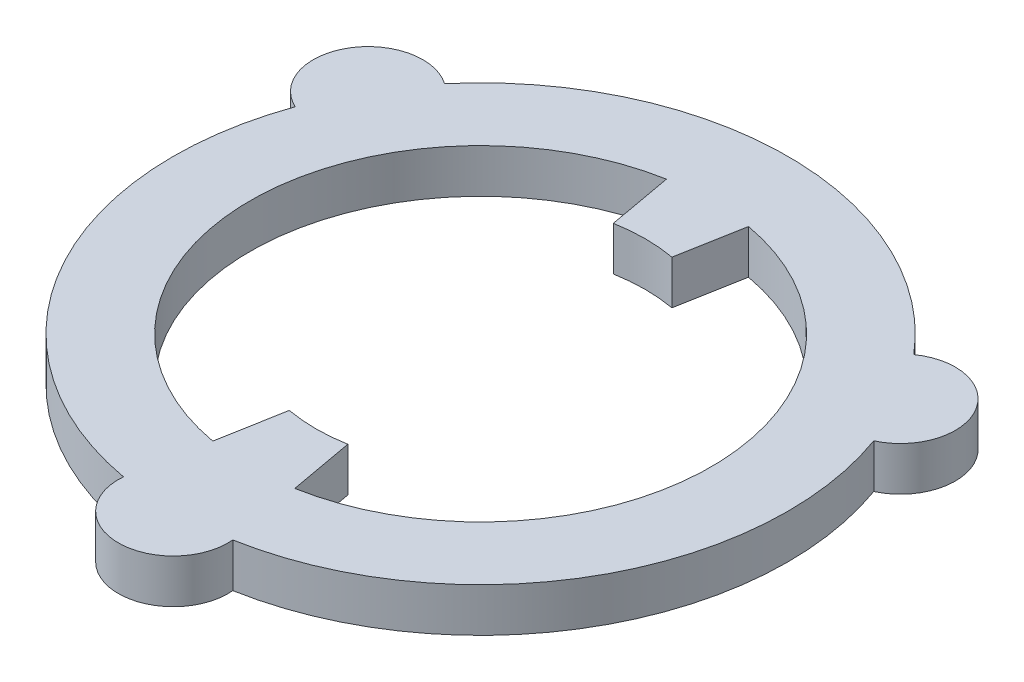
SolidWorks part; units mm, degrees
ref_plane "Planta" through (0, 0, 0) normal (0, 0, 1) x (1, 0, 0)
ref_plane "Alzado" through (0, 0, 0) normal (0, 1, 0) x (1, 0, 0)
ref_plane "Vista lateral" through (0, 0, 0) normal (1, 0, 0) x (0, 0, -1)
sketch "Croquis1" plane through (0, 0, 0) normal (0, 1, 0) x (1, 0, 0)
  line L0 (0, -9.3154) -> (0, -7.5) construction
  line L1 (0, 0) -> (-6.4952, 3.75) construction
  line L2 (0, 0) -> (12.1244, 7) construction
  line L4 (1.8675, -10.3326) -> (1.3339, -7.3804)
  line L5 (-1.3339, -7.3804) -> (-1.8675, -10.3326)
  line L7 (-1.8675, 10.3326) -> (-1.3339, 7.3804)
  line L8 (1.3339, 7.3804) -> (1.8675, 10.3326)
  line L11 (-9.0933, 5.25) -> (-12.1244, 7) construction
  arc A0 (-13.1761, 4.732) -> (-2.49, -13.7768) centre (0, 0) ccw
  arc A1 (-2.49, -13.7768) -> (2.49, -13.7768) centre (0, -14) ccw
  arc A2 (10.686, 9.0448) -> (-10.686, 9.0448) centre (0, 0) ccw
  arc A3 (13.1761, 4.732) -> (10.686, 9.0448) centre (12.1244, 7) ccw
  arc A4 (-10.686, 9.0448) -> (-13.1761, 4.732) centre (-12.1244, 7) ccw
  arc A5 (2.49, -13.7768) -> (13.1761, 4.732) centre (0, 0) ccw
  arc A6 (1.8675, -10.3326) -> (1.8675, 10.3326) centre (0, 0) ccw
  arc A7 (-1.3339, -7.3804) -> (1.3339, -7.3804) centre (0, 0) ccw
  arc A8 (1.3339, 7.3804) -> (-1.3339, 7.3804) centre (0, 0) ccw
  arc A9 (-1.8675, 10.3326) -> (-1.8675, -10.3326) centre (0, 0) ccw
  dimension "D1" = 2.5
  dimension "D2" = 2.5
  dimension "D3" = 2.5
  dimension "D4" = 28
  dimension "D7" = 21
  dimension "D8" = 15
  dimension "D5" = 120
  dimension "D6" = 120
extrude "Saliente-Extruir1" add sketch "Croquis1" along normal blind 2
